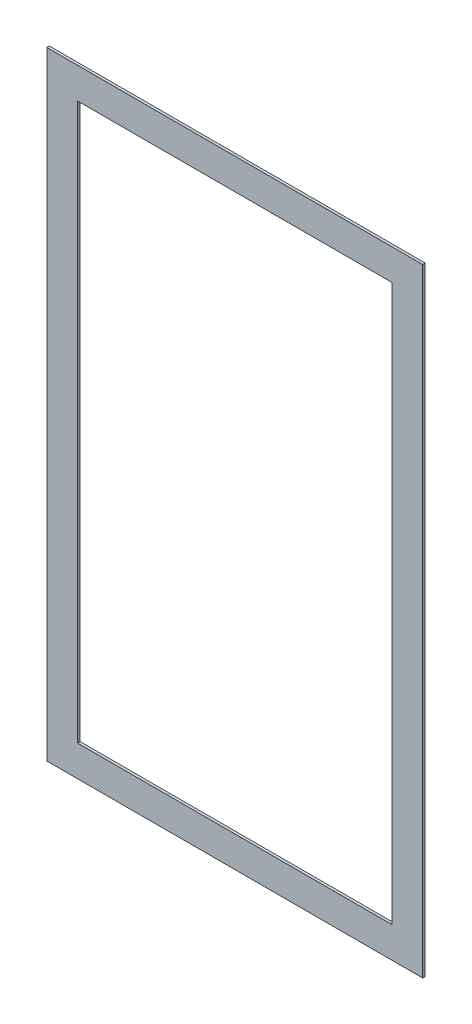
SolidWorks part; units mm, degrees
ref_plane "Front Plane" through (0, 0, 0) normal (0, 0, 1) x (1, 0, 0)
ref_plane "Top Plane" through (0, 0, 0) normal (0, 1, 0) x (1, 0, 0)
ref_plane "Right Plane" through (0, 0, 0) normal (1, 0, 0) x (0, 0, -1)
sketch "Sketch2" plane through (0, 0, 0) normal (0, 0, 1) x (1, 0, 0)
  line L1 (387.35, -685.8) -> (-387.35, -685.8)
  line L2 (387.35, -685.8) -> (387.35, 685.8)
  line L3 (387.35, 685.8) -> (-387.35, 685.8)
  line L4 (-387.35, -685.8) -> (-387.35, 685.8)
  line L5 (387.35, -685.8) -> (-387.35, 685.8) construction
  line L6 (387.35, 685.8) -> (-387.35, -685.8) construction
  line L7 (463.55, -762) -> (-463.55, -762)
  line L8 (463.55, -762) -> (463.55, 762)
  line L9 (463.55, 762) -> (-463.55, 762)
  line L10 (-463.55, -762) -> (-463.55, 762)
  line L11 (463.55, -762) -> (-463.55, 762) construction
  line L12 (463.55, 762) -> (-463.55, -762) construction
  point P0 (0, 0)
  point P6 (0, 0)
  dimension "D1" = 1371.6
  dimension "D2" = 774.7
  dimension "D3" = 1524
  dimension "D4" = 927.1
extrude "Boss-Extrude1" add sketch "Sketch2" along normal blind 6.35
